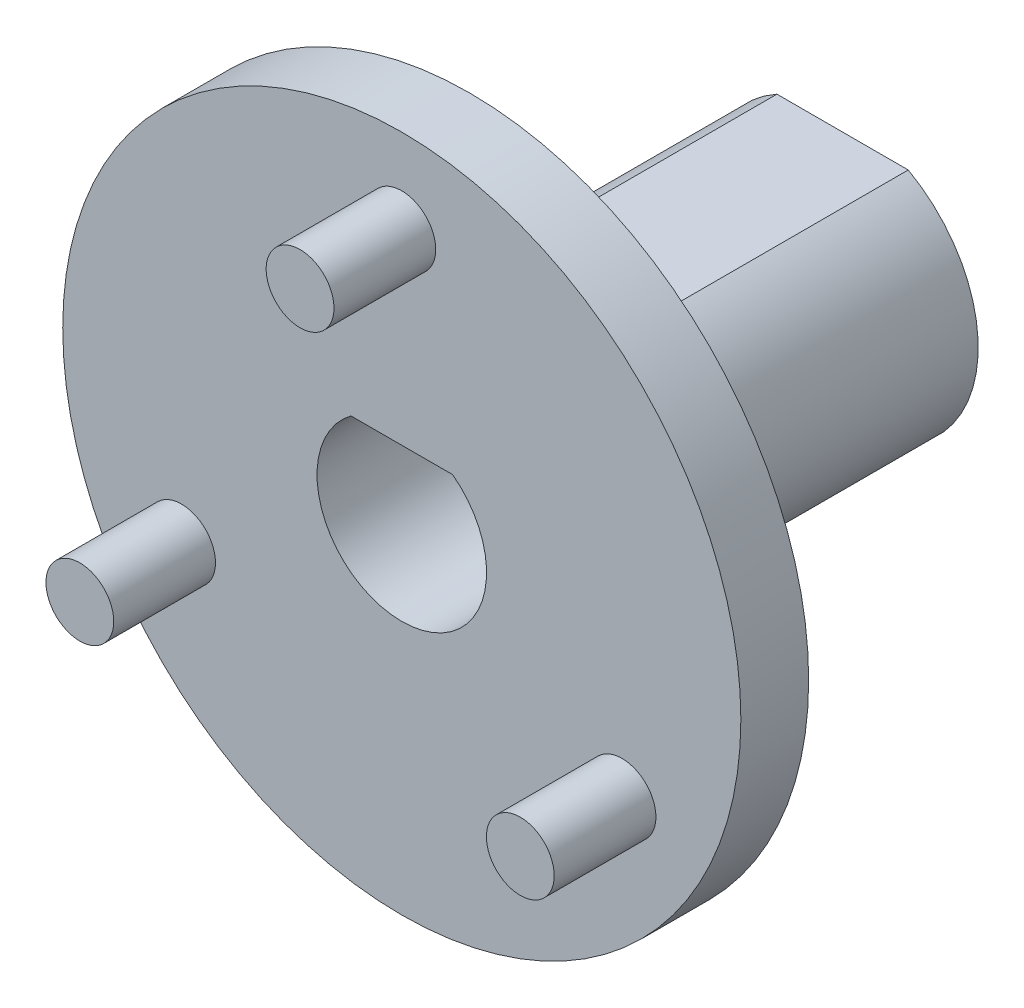
SolidWorks part; units mm, degrees
ref_plane "前视基准面" through (0, 0, 0) normal (0, 0, 1) x (1, 0, 0)
ref_plane "上视基准面" through (0, 0, 0) normal (0, 1, 0) x (1, 0, 0)
ref_plane "右视基准面" through (0, 0, 0) normal (1, 0, 0) x (0, 0, -1)
sketch "草图1" plane through (0, 0, 0) normal (0, 0, 1) x (1, 0, 0)
  circle A3 centre (0, 0) radius 7.5 construction
  circle A4 centre (0, 7.5) radius 1
  circle A5 centre (6.4952, -3.75) radius 1
  circle A6 centre (-6.4952, -3.75) radius 1
  point P8 (0, 0)
  dimension "D1" = 15
  dimension "D2" = 2
extrude "凸台-拉伸1" add sketch "草图1" along normal blind 3
sketch "草图2" plane through (0, 0, 0) normal (0, 0, -1) x (-1, 0, 0)
  circle A1 centre (0, 0) radius 10
  dimension "D1" = 20
extrude "凸台-拉伸2" add sketch "草图2" along normal blind 2
sketch "草图3" plane through (0, 0, -2) normal (0, 0, -1) x (-1, 0, 0)
  circle A0 centre (0, 0) radius 5
  dimension "D1" = 10
extrude "凸台-拉伸3" add sketch "草图3" along normal blind 1
sketch "草图4" plane through (0, 0, -3) normal (0, 0, -1) x (-1, 0, 0)
  line L0 (-1.9365, 3.5) -> (1.9365, 3.5)
  arc A0 (-1.9365, 3.5) -> (1.9365, 3.5) centre (0, 0) ccw
  dimension "D1" = 8
  dimension "D2" = 3.5
extrude "凸台-拉伸4" add sketch "草图4" along normal blind 10
sketch "草图5" plane through (0, 0, -13) normal (0, 0, -1) x (-1, 0, 0)
  line L0 (-1.5, 2) -> (1.5, 2)
  arc A0 (-1.5, 2) -> (1.5, 2) centre (0, 0) ccw
  dimension "D1" = 5
  dimension "D2" = 2
extrude "切除-拉伸1" cut sketch "草图5" against normal blind 24
